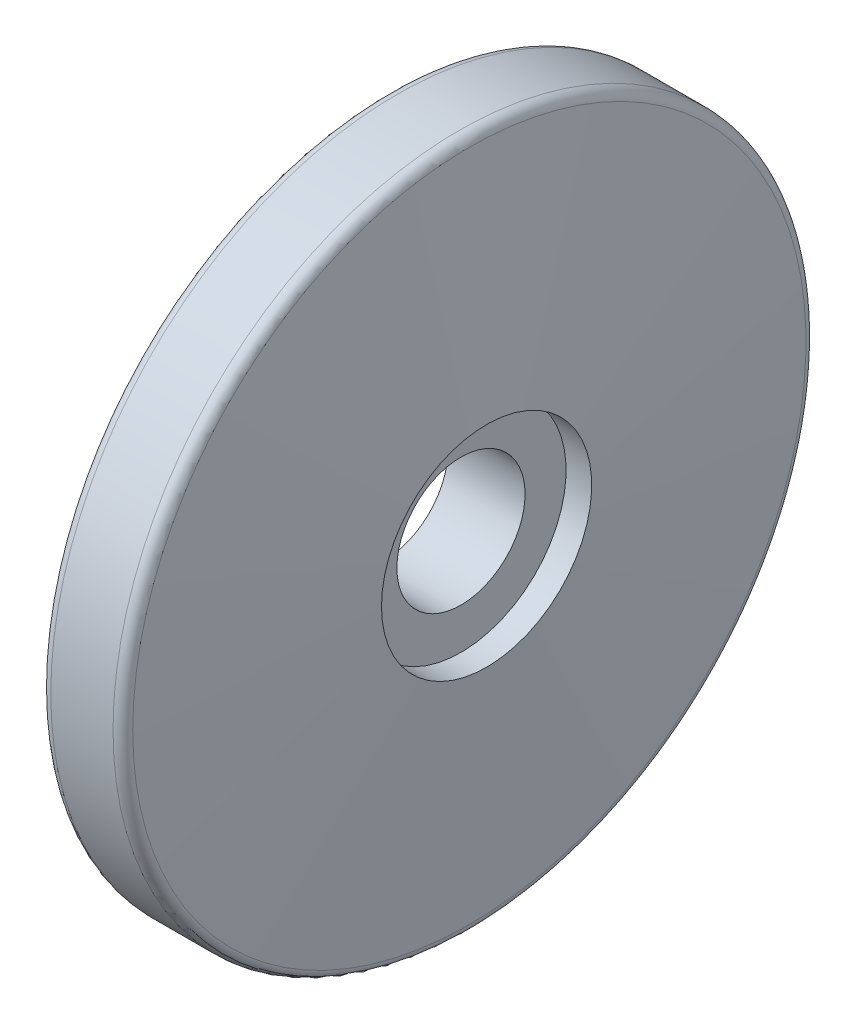
SolidWorks part; units mm, degrees
material "1060 Сплав"
ref_plane "Спереди" through (0, 0, 0) normal (0, 0, 1) x (1, 0, 0)
ref_plane "Сверху" through (0, 0, 0) normal (0, 1, 0) x (1, 0, 0)
ref_plane "Справа" through (0, 0, 0) normal (1, 0, 0) x (0, 0, -1)
sketch "Эскиз1" plane through (0, 0, 0) normal (0, 0, 1) x (1, 0, 0)
  line L0 (-643.3327, 0) -> (31523.3015, 0) construction
  line L1 (6.4283, 12.5) -> (-8.5717, 12.5)
  line L2 (-8.5717, 12.5) -> (-8.5717, 26)
  line L3 (-8.5717, 26) -> (-13.0717, 26)
  line L4 (-13.0717, 26) -> (-13.0717, 30)
  line L5 (-13.0717, 30) -> (-8.0717, 30)
  line L6 (-8.0717, 30) -> (-8.0717, 65.5)
  line L7 (-6.0717, 67.5) -> (6.0717, 67.5)
  line L8 (8.0662, 65.6485) -> (11.4283, 20.5)
  line L9 (11.4283, 20.5) -> (6.4283, 20.5)
  line L10 (6.4283, 20.5) -> (6.4283, 12.5)
  arc A0 (6.0717, 67.5) -> (8.0662, 65.6485) centre (6.0717, 65.5) cw
  arc A1 (-8.0717, 65.5) -> (-6.0717, 67.5) centre (-6.0717, 65.5) cw
  point P12 (0, 67.5)
  point P17 (7.9283, 67.5)
  point P20 (-8.0717, 67.5)
  dimension "D11" = 2
  dimension "D1" = 25
  dimension "D2" = 52
  dimension "D3" = 60
  dimension "D4" = 4.5
  dimension "D5" = 19.5
  dimension "D6" = 5
  dimension "D7" = 16
  dimension "D8" = 5
  dimension "D9" = 135
  dimension "D10" = 41
revolve "Повернуть1" add sketch "Эскиз1" angle 360 about L0
